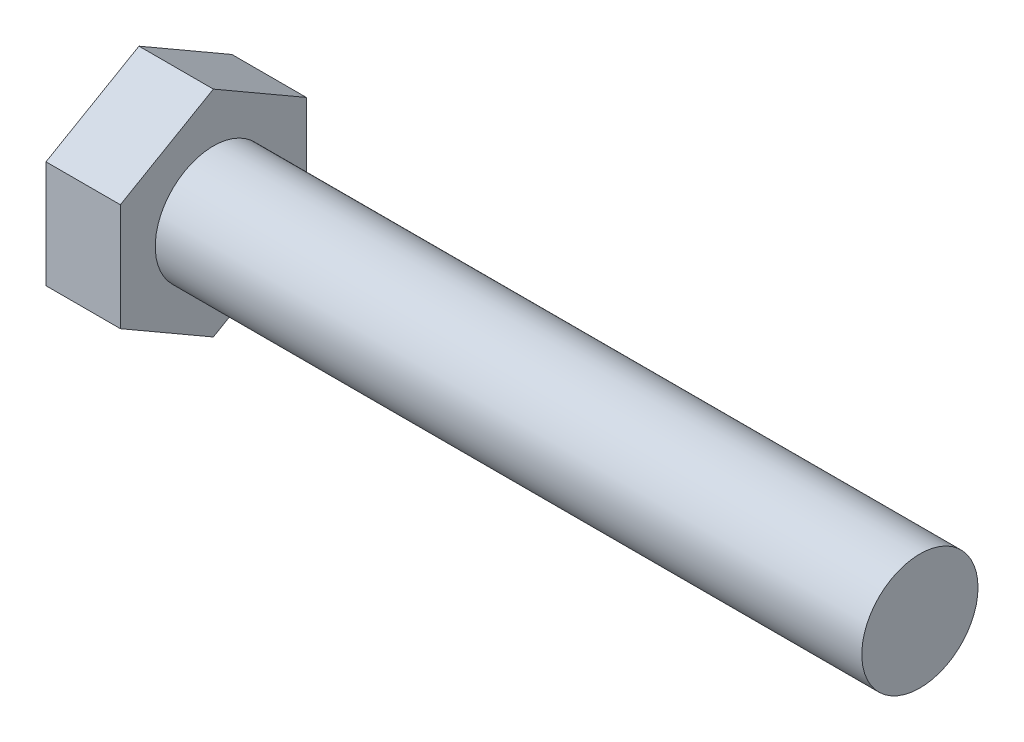
SolidWorks part; units mm, degrees
ref_plane "Front Plane" through (0, 0, 0) normal (0, 0, 1) x (1, 0, 0)
ref_plane "Top Plane" through (0, 0, 0) normal (0, 1, 0) x (1, 0, 0)
ref_plane "Right Plane" through (0, 0, 0) normal (1, 0, 0) x (0, 0, -1)
sketch "Sketch1" plane through (0, 0, 0) normal (1, 0, 0) x (0, 0, -1)
  line L1 (6.35, 3.6662) -> (0, 7.3323)
  line L2 (0, 7.3323) -> (-6.35, 3.6662)
  line L3 (-6.35, 3.6662) -> (-6.35, -3.6662)
  line L4 (-6.35, -3.6662) -> (0, -7.3323)
  line L5 (0, -7.3323) -> (6.35, -3.6662)
  line L6 (6.35, -3.6662) -> (6.35, 3.6662)
  circle A0 centre (0, 0) radius 6.35 construction
  point P1 (3.175, -5.4993)
  dimension "D1" = 6.35
  dimension "D2" = 7.3323
extrude "Boss-Extrude1" add sketch "Sketch1" along normal blind 5.08
sketch "Sketch2" plane through (5.08, 0, 0) normal (1, 0, 0) x (0, 0, -1)
  circle A0 centre (0, 0) radius 3.9688
  dimension "D1" = 7.9375
extrude "Boss-Extrude2" add sketch "Sketch2" along normal blind 48.26
